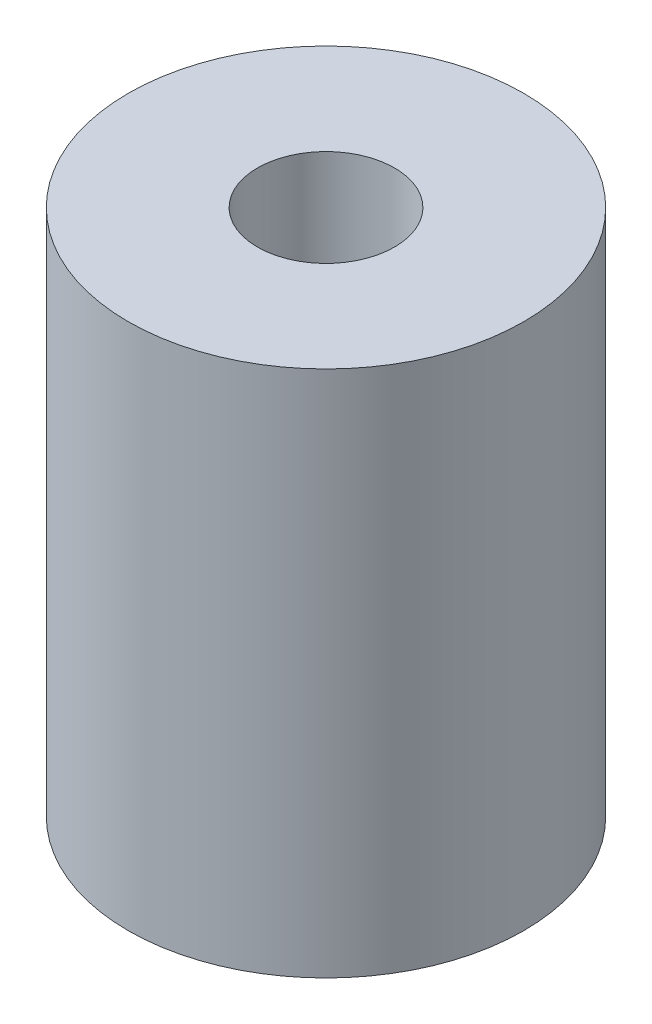
SolidWorks part; units mm, degrees
ref_plane "Front Plane" through (0, 0, 0) normal (0, 0, 1) x (1, 0, 0)
ref_plane "Top Plane" through (0, 0, 0) normal (0, 1, 0) x (1, 0, 0)
ref_plane "Right Plane" through (0, 0, 0) normal (1, 0, 0) x (0, 0, -1)
sketch "Sketch1" plane through (0, 0, 0) normal (0, 1, 0) x (1, 0, 0)
  circle A0 centre (0, 0) radius 9.525
  circle A1 centre (0, 0) radius 3.302
extrude "Boss-Extrude1" add sketch "Sketch1" along normal blind 25.4
